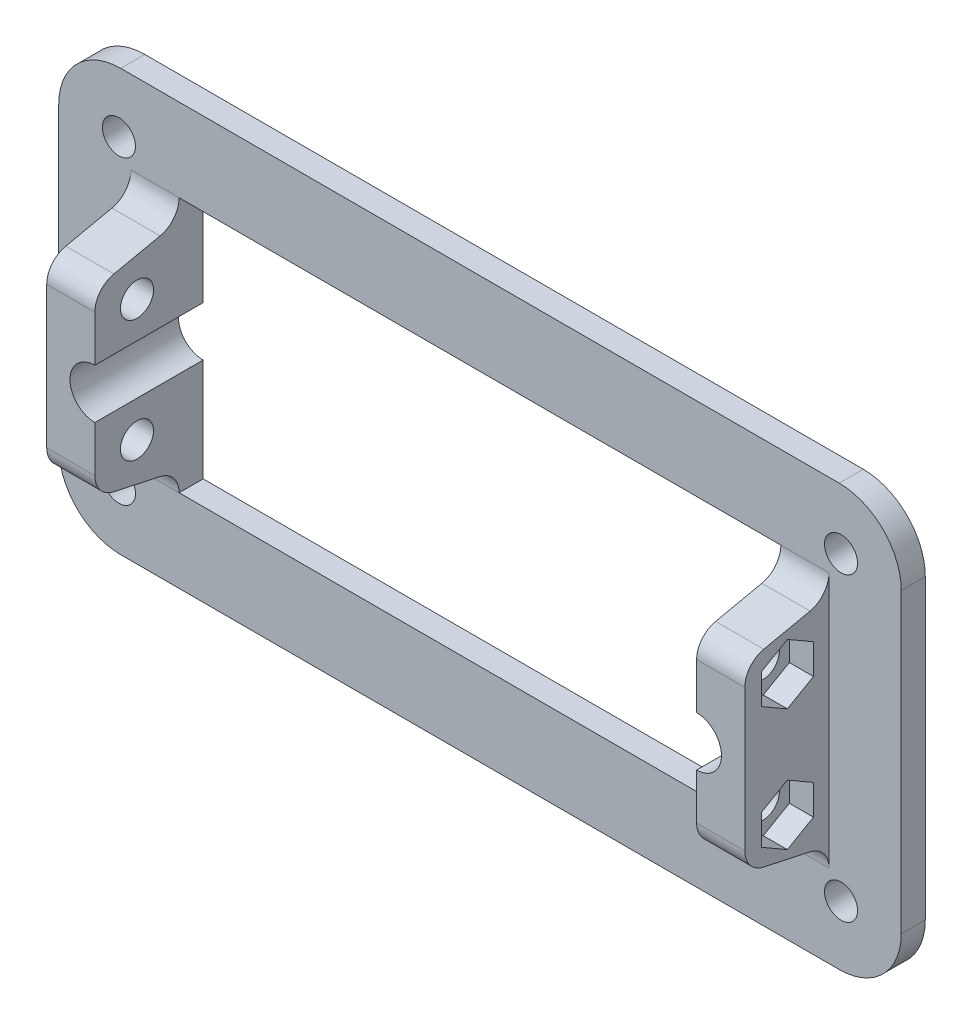
SolidWorks part; units mm, degrees
material "ABS"
ref_plane "Front Plane" through (0, 0, 0) normal (0, 0, 1) x (1, 0, 0)
ref_plane "Top Plane" through (0, 0, 0) normal (0, 1, 0) x (1, 0, 0)
ref_plane "Right Plane" through (0, 0, 0) normal (1, 0, 0) x (0, 0, -1)
sketch "Sketch1" plane through (0, 0, 0) normal (0, 0, 1) x (1, 0, 0)
  line L0 (0, 35) -> (140, 35) construction
  line L1 (0, 0) -> (140, 0)
  line L2 (0, 0) -> (0, 70)
  line L3 (0, 70) -> (140, 70)
  line L4 (140, 0) -> (140, 70)
  line L5 (20, 56.23) -> (120, 56.23)
  line L6 (20, 56.23) -> (20, 13.77)
  line L7 (20, 13.77) -> (120, 13.77)
  line L8 (120, 56.23) -> (120, 13.77)
  line L9 (70, 70) -> (70, 0) construction
  circle A0 centre (10, 60) radius 2.75
  circle A1 centre (130, 60) radius 2.75
  circle A2 centre (10, 10) radius 2.75
  circle A3 centre (130, 10) radius 2.75
  circle A4 centre (10.3009, 59.6991) radius 10.3009
  circle A5 centre (10.3009, 10.3009) radius 10.3009
  circle A6 centre (129.6991, 59.6991) radius 10.3009
  circle A7 centre (129.6991, 10.3009) radius 10.3009
  dimension "D8" = 10
  dimension "D9" = 5.5
  dimension "D1" = 70
  dimension "D2" = 140
  dimension "D3" = 13.77
  dimension "D4" = 13.77
  dimension "D5" = 100
  dimension "D6" = 20
  dimension "D7" = 10
extrude "Boss-Extrude2" add sketch "Sketch1" along normal blind 4 contours A4 A0 | A6 L3 A4 L5 | A5 L6 A4 L2 | A5 A2 | A7 L7 A5 L1 | A7 A3 | A7 L4 A6 L8 | A6 A1
sketch "Sketch4" plane through (0, 0, 4) normal (0, 0, 1) x (1, 0, 0)
  line L0 (20, 13.77) -> (120, 13.77) construction
  line L1 (20, 56.23) -> (12, 56.23)
  line L2 (20, 56.23) -> (20, 13.77)
  line L3 (20, 13.77) -> (12, 13.77)
  line L4 (12, 56.23) -> (12, 13.77)
  line L5 (120, 56.23) -> (128, 56.23)
  line L6 (120, 56.23) -> (120, 13.77)
  line L7 (120, 13.77) -> (128, 13.77)
  line L8 (128, 56.23) -> (128, 13.77)
  dimension "D1" = 8
  dimension "D2" = 8
extrude "Boss-Extrude3" add sketch "Sketch4" along normal blind 14
sketch "Sketch5" plane through (0, 0, 18) normal (0, 0, 1) x (1, 0, 0)
  line L0 (20, 13.77) -> (20, 56.23) construction
  line L1 (120, 56.23) -> (120, 13.77) construction
  circle A0 centre (20, 35) radius 4.125
  circle A1 centre (120, 35) radius 4.125
  dimension "D1" = 8.25
  dimension "D2" = 8.25
extrude "Cut-Extrude2" cut sketch "Sketch5" against normal through all
sketch "Sketch7" plane through (20, 0, 0) normal (1, 0, 0) x (0, 0, -1)
  line L0 (-18, 13.77) -> (-18, 30.875) construction
  line L1 (-18, 30.875) -> (0, 30.875) construction
  line L3 (-18, 39.125) -> (-18, 56.23) construction
  line L4 (0, 39.125) -> (-18, 39.125) construction
  circle A0 centre (-11, 24.875) radius 2.75
  circle A1 centre (-11, 45.125) radius 2.75
  dimension "D1" = 7
  dimension "D2" = 6
  dimension "D3" = 5.5
  dimension "D4" = 7
  dimension "D5" = 6
  dimension "D6" = 5.5
extrude "Cut-Extrude3" cut sketch "Sketch7" against normal blind 4
sketch "Sketch8" plane through (120, 0, 0) normal (-1, 0, 0) x (0, 0, 1)
  line L0 (18, 30.875) -> (0, 30.875) construction
  line L1 (18, 30.875) -> (18, 13.77) construction
  line L2 (18, 56.23) -> (18, 39.125) construction
  line L3 (0, 39.125) -> (18, 39.125) construction
  circle A0 centre (11, 24.875) radius 2.75
  circle A1 centre (11, 45.125) radius 2.75
  dimension "D1" = 6
  dimension "D2" = 7
  dimension "D3" = 5.5
  dimension "D4" = 7
  dimension "D5" = 6
  dimension "D6" = 5.5
extrude "Cut-Extrude4" cut sketch "Sketch8" against normal blind 4
sketch "Sketch11" plane through (16, 0, 0) normal (1, 0, 0) x (0, 0, -1)
  point P0 (-11, 24.875)
sketch "Sketch12" plane through (12, 0, 0) normal (-1, 0, 0) x (0, 0, 1)
  line L0 (10.9199, 19.875) -> (15.25, 22.375)
  line L1 (11, 24.875) -> (18, 24.875) construction
  line L2 (15.25, 22.375) -> (15.25, 27.375)
  line L3 (18, 35) -> (4, 35) construction
  line L4 (18, 56.23) -> (18, 13.77) construction
  line L5 (4, 56.23) -> (4, 13.77) construction
  line L6 (15.25, 27.375) -> (10.9199, 29.875)
  line L7 (10.9199, 29.875) -> (6.5897, 27.375)
  line L8 (6.5897, 27.375) -> (6.5897, 22.375)
  line L9 (6.5897, 22.375) -> (10.9199, 19.875)
  line L10 (10.9199, 40.125) -> (6.5897, 42.625)
  line L11 (15.25, 42.625) -> (10.9199, 40.125)
  line L12 (15.25, 47.625) -> (15.25, 42.625)
  line L13 (10.9199, 50.125) -> (15.25, 47.625)
  line L14 (6.5897, 47.625) -> (10.9199, 50.125)
  line L15 (6.5897, 42.625) -> (6.5897, 47.625)
  dimension "D2" = 2.5
  dimension "D3" = 5
  dimension "D4" = 5
  dimension "D5" = 120
  dimension "D6" = 2.75
  dimension "D7" = 5
  dimension "D8" = 120
  dimension "D9" = 5
  dimension "D10" = 120
  dimension "D11" = 5
extrude "Cut-Extrude8" cut sketch "Sketch12" against normal blind 4
sketch "Sketch15" plane through (128, 0, 0) normal (1, 0, 0) x (0, 0, -1)
  line L0 (-18, 35) -> (-4, 35) construction
  line L1 (-18, 13.77) -> (-18, 56.23) construction
  line L2 (-4, 13.77) -> (-4, 56.23) construction
  line L3 (-11, 24.875) -> (-18, 24.875) construction
  line L4 (-10.9199, 19.875) -> (-15.25, 22.375)
  line L5 (-15.25, 22.375) -> (-15.25, 27.375)
  line L6 (-15.25, 27.375) -> (-10.9199, 29.875)
  line L7 (-10.9199, 29.875) -> (-6.5897, 27.375)
  line L8 (-6.5897, 27.375) -> (-6.5897, 22.375)
  line L9 (-6.5897, 22.375) -> (-10.9199, 19.875)
  line L10 (-10.9199, 19.875) -> (-10.9033, 19.8938)
  line L11 (-15.25, 47.625) -> (-15.25, 42.625)
  line L12 (-10.9199, 50.125) -> (-15.25, 47.625)
  line L13 (-6.5897, 47.625) -> (-10.9199, 50.125)
  line L14 (-6.5897, 42.625) -> (-6.5897, 47.625)
  line L15 (-10.9199, 40.125) -> (-6.5897, 42.625)
  line L16 (-15.25, 42.625) -> (-10.9199, 40.125)
  circle A0 centre (-11, 24.875) radius 2.75
  dimension "D1" = 5.5
  dimension "D2" = 10.125
  dimension "D3" = 7
  dimension "D7" = 120
  dimension "D4" = 5
  dimension "D5" = 2.5
  dimension "D6" = 5
  dimension "D8" = 2.75
  dimension "D9" = 5
  dimension "D10" = 120
  dimension "D11" = 5
  dimension "D12" = 5
extrude "Cut-Extrude9" cut sketch "Sketch15" against normal blind 4
sketch "Sketch16" plane through (12, 0, 0) normal (-1, 0, 0) x (0, 0, 1)
  line L1 (4, 10.3009) -> (4, 59.6991) construction
  line L2 (18, 56.23) -> (18, 13.77) construction
  line L3 (7.1622, 52.3187) -> (14.8378, 50.6746)
  line L4 (14.8378, 50.6746) -> (14.8298, 50.6413)
  line L5 (18, 35) -> (4, 35) construction
  line L6 (4, 56.23) -> (4, 13.77) construction
  line L7 (7.1622, 17.6813) -> (14.8378, 19.3254)
  line L8 (7.1622, 52.3187) -> (14.8378, 50.6746)
  arc A0 (18, 23.2367) -> (14.8378, 19.3254) centre (14, 23.2367) cw
  arc A1 (4, 13.77) -> (7.1622, 17.6813) centre (8, 13.77) cw
  arc A2 (4, 56.23) -> (7.1622, 52.3187) centre (8, 56.23) ccw
  arc A3 (18, 46.7633) -> (14.8378, 50.6746) centre (14, 46.7633) ccw
  line M15 (4, 13.77) -> (18, 13.77)
  line M16 (18, 13.77) -> (18, 56.23)
  line M17 (18, 56.23) -> (4, 56.23)
  dimension "D5" = 4
  dimension "D6" = 4
  dimension "D7" = 102.09
extrude "Cut-Extrude12" cut sketch "Sketch16" against normal through all contours A1 A0 L7 M15 M16 | A3 A2 L3 M16 M17
